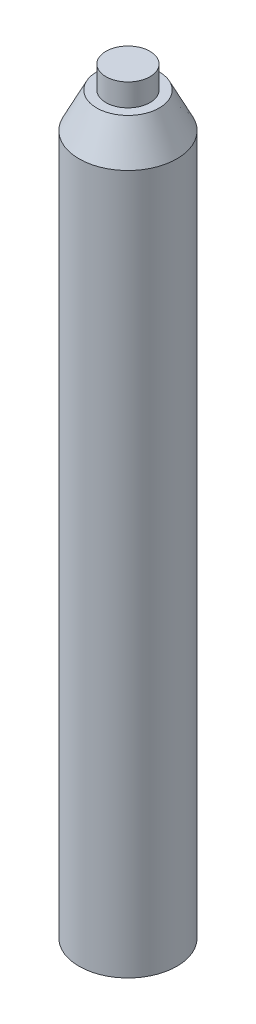
SolidWorks part; units mm, degrees
material "1060 Alloy"
ref_plane "Front Plane" through (0, 0, 0) normal (0, 0, 1) x (1, 0, 0)
ref_plane "Top Plane" through (0, 0, 0) normal (0, 1, 0) x (1, 0, 0)
ref_plane "Right Plane" through (0, 0, 0) normal (1, 0, 0) x (0, 0, -1)
sketch "Sketch1" plane through (0, 0, 0) normal (0, 0, 1) x (1, 0, 0)
  line L0 (0, 0) -> (-5.55, 0)
  line L1 (-5.55, 0) -> (-5.55, 79.37)
  line L2 (-5.55, 79.37) -> (-3.55, 83.37)
  line L3 (-3.55, 83.37) -> (-2.5, 83.37)
  line L4 (-2.5, 83.37) -> (-2.5, 85.92)
  line L5 (-2.5, 85.92) -> (0, 85.92)
  line L6 (0, 85.92) -> (0, 0)
  dimension "D1" = 83.37
  dimension "D2" = 4
  dimension "D3" = 2.55
  dimension "D4" = 5.55
  dimension "D5" = 2
  dimension "D6" = 2.5
ref_axis "Axis1" through (0, 90.216, 0) along (0, -1, 0)
revolve "Revolve1" add sketch "Sketch1" angle 360 about axis through (0, 90.216, 0) along (0, -1, 0)
hole_wizard "#6 (0.204) Diameter Hole1" positions "Sketch3" profile "Sketch2" hole size "#6" standard "Ansi Inch"
sketch "Sketch3" plane through (0, 0, 0) normal (0, -1, 0) x (1, 0, 0)
  line L0 (0, 5.55) -> (0, -5.55) construction
  circle A0 centre (0, 0) radius 5.55 construction
  point P0 (0, 0)
sketch "Sketch2" plane through (0, 0, 0) normal (1, 0, 0) x (0, 0, -1)
  line L0 (0, 0) -> (0, 11.5567)
  line L1 (0, 11.5567) -> (2.5908, 10)
  line L2 (2.5908, 10) -> (2.5908, 0)
  line L5 (2.5908, 0) -> (0, 0)
  line L10 (0, 11.5567) -> (-2.5908, 10) construction
  line L11 (0, -6.35) -> (0, 107.95) construction
  dimension "Hole Dia." = 5.1816
  dimension "Hole Depth" = 10
  dimension "Drill Angle" = 118
